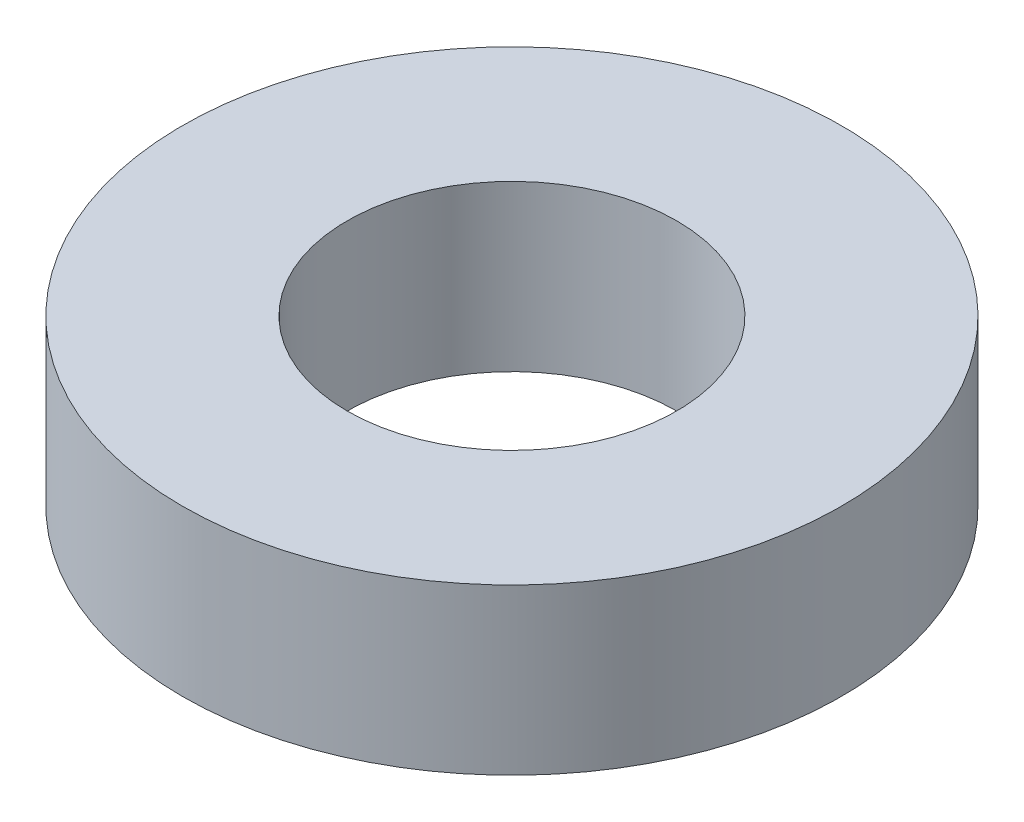
SolidWorks part; units mm, degrees
material "Rubber"
ref_plane "Front" through (0, 0, 0) normal (0, 0, 1) x (1, 0, 0)
ref_plane "Top" through (0, 0, 0) normal (0, 1, 0) x (1, 0, 0)
ref_plane "Right" through (0, 0, 0) normal (1, 0, 0) x (0, 0, -1)
sketch "Sketch1" plane through (0, 0, 0) normal (0, 1, 0) x (1, 0, 0)
  circle A0 centre (0, 0) radius 3.175
  circle A1 centre (0, 0) radius 1.5875
  dimension "D1" = 3.175
  dimension "D2" = 1.5875
extrude "Boss-Extrude1" add sketch "Sketch1" along normal mid plane 1.5875
